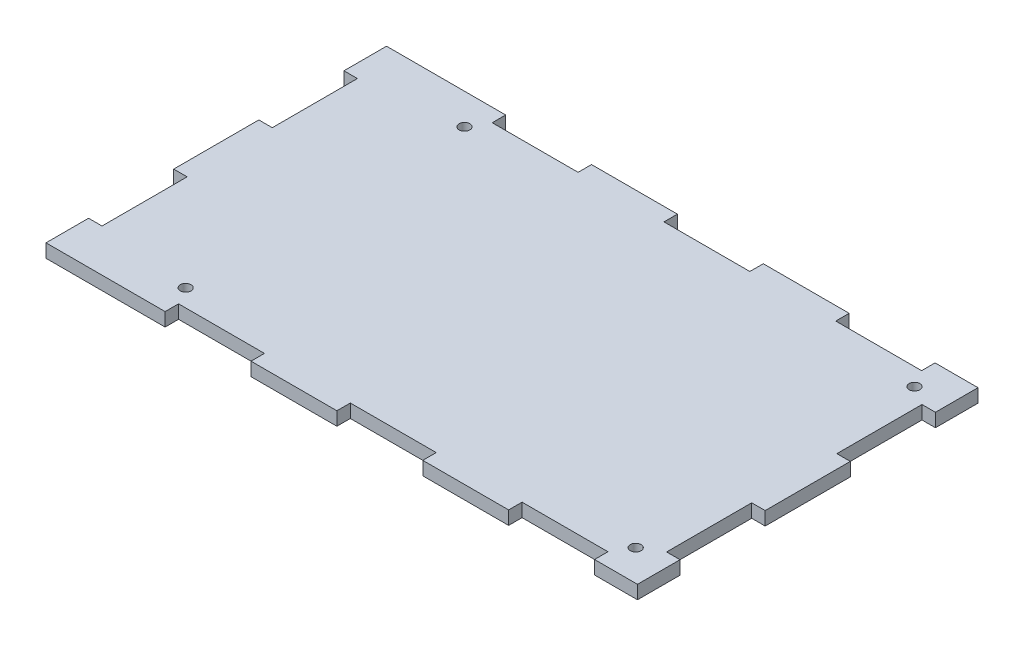
SolidWorks part; units mm, degrees
material "Acrílico (Impacto medio-alto)"
ref_plane "Alzado" through (0, 0, 0) normal (0, 0, 1) x (1, 0, 0)
ref_plane "Planta" through (0, 0, 0) normal (0, 1, 0) x (1, 0, 0)
ref_plane "Vista lateral" through (0, 0, 0) normal (1, 0, 0) x (0, 0, -1)
sketch "Croquis1" plane through (0, 0, 0) normal (0, 1, 0) x (1, 0, 0)
  line L1 (-57.5, -38) -> (57.5, -38)
  line L2 (-57.5, -38) -> (-57.5, 38)
  line L3 (-57.5, 38) -> (57.5, 38)
  line L4 (57.5, -38) -> (57.5, 38)
  line L5 (-57.5, -38) -> (57.5, 38) construction
  line L6 (-57.5, 38) -> (57.5, -38) construction
  point P0 (0, 0)
  dimension "D1" = 115
  dimension "D2" = 76
extrude "Saliente-Extruir1" add sketch "Croquis1" along normal mid plane 3
sketch "Croquis3" plane through (0, 0, 0) normal (0, 1, 0) x (1, 0, 0)
  line L0 (-57.5, -38) -> (57.5, -38) construction
  line L1 (-47.9167, -35) -> (-39.4833, -35)
  line L2 (-47.9167, -35) -> (-47.9167, -38)
  line L3 (-47.9167, -38) -> (-28.75, -38)
  line L4 (-28.75, -35) -> (-28.75, -38)
  line L5 (-39.4833, -35) -> (-39.4833, -32) construction
  line L6 (-57.5, 38) -> (-57.5, -38) construction
  line L7 (-39.4833, -32) -> (-37.1833, -32) construction
  line L8 (-37.1833, -32) -> (-37.1833, -35) construction
  line L10 (-37.1833, -35) -> (-28.75, -35)
  line L12 (-39.4833, -35) -> (-37.1833, -35)
  point P12 (-38.3333, -32)
  point P15 (-38.3333, -38)
  dimension "D2" = 3
  dimension "D3" = 9.5833
  dimension "D1" = 19.1667
  dimension "D4" = 2.3
  dimension "D5" = 3
extrude "Cortar-Extruir2" cut sketch "Croquis3" against normal through all both and the other way through all
pattern_linear "MatrizL4" count 3 spacing 38.3333 along (1, 0, 0) of "Cortar-Extruir2"
mirror "Simetría1" about plane through (0, 0, 0) normal (0, 0, 1) of "MatrizL4", "Cortar-Extruir2"
sketch "Croquis4" plane through (0, 0, 0) normal (0, 1, 0) x (1, 0, 0)
  line L0 (-57.5, 38) -> (-57.5, -38) construction
  line L1 (-57.5, 28.5) -> (-54.5, 28.5)
  line L2 (-57.5, 28.5) -> (-57.5, 9.5)
  line L3 (-57.5, 9.5) -> (-54.5, 9.5)
  line L4 (-54.5, 28.5) -> (-54.5, 20.15)
  line L5 (-47.9167, 38) -> (-57.5, 38) construction
  line L6 (-54.5, 17.85) -> (-51.5, 17.85) construction
  line L7 (-51.5, 17.85) -> (-51.5, 20.15) construction
  line L8 (-51.5, 20.15) -> (-54.5, 20.15) construction
  line L9 (-54.5, 17.85) -> (-54.5, 9.5)
  line L10 (-54.5, 20.15) -> (-54.5, 17.85)
  point P12 (-51.5, 19)
  point P13 (-57.5, 19)
  dimension "D1" = 3
  dimension "D4" = 2.3
  dimension "D5" = 3
  dimension "D2" = 9.5
  dimension "D3" = 19
extrude "Cortar-Extruir3" cut sketch "Croquis4" against normal through all both and the other way through all
pattern_linear "MatrizL5" count 2 spacing 38 along (0, 0, 1) of "Cortar-Extruir3"
mirror "Simetría2" about plane through (0, 0, 0) normal (1, 0, 0) of "MatrizL5", "Cortar-Extruir3"
sketch "Croquis2" plane through (0, 0, 0) normal (0, 1, 0) x (1, 0, 0)
  line L0 (0, 10) -> (0, 0) construction
  line L2 (0, 0) -> (-10, 0) construction
  circle A0 centre (-50.22, 31.115) radius 1.2
  circle A1 centre (-50.22, -31.115) radius 1.2
  circle A2 centre (50.22, 31.115) radius 1.2
  circle A3 centre (50.22, -31.115) radius 1.2
  dimension "D1" = 2.4
  dimension "D2" = 100.44
  dimension "D3" = 62.23
  dimension "D4" = 10
extrude "Cortar-Extruir1" cut sketch "Croquis2" against normal through all both and the other way through all
sketch "Croquis5" plane through (-57.5, 0, 0) normal (-1, 0, 0) x (0, 0, 1)
  line L0 (-38, -1.5) -> (-28.5, -1.5) construction
  line L1 (-28.5, -1.5) -> (-28.5, 1.5) construction
  line L2 (-28.5, 1.5) -> (-38, 1.5) construction
  line L3 (-38, 1.5) -> (-38, -1.5) construction
  line L4 (38, 1.5) -> (28.5, 1.5) construction
  line L5 (28.5, 1.5) -> (28.5, -1.5) construction
  line L6 (28.5, -1.5) -> (38, -1.5) construction
  line L7 (38, -1.5) -> (38, 1.5) construction
  line L8 (-38, -1.5) -> (-28.5, -1.5)
  line L9 (-28.5, -1.5) -> (-28.5, 1.5)
  line L10 (-28.5, 1.5) -> (-38, 1.5)
  line L11 (-38, 1.5) -> (-38, -1.5)
  line L12 (38, 1.5) -> (28.5, 1.5)
  line L13 (28.5, 1.5) -> (28.5, -1.5)
  line L14 (28.5, -1.5) -> (38, -1.5)
  line L15 (38, -1.5) -> (38, 1.5)
  line L20 (-9.5, -1.5) -> (9.5, -1.5)
  line L21 (9.5, -1.5) -> (9.5, 1.5)
  line L22 (9.5, 1.5) -> (-9.5, 1.5)
  line L23 (-9.5, 1.5) -> (-9.5, -1.5)
  line L24 (-9.5, -1.5) -> (9.5, -1.5)
  line L25 (9.5, -1.5) -> (9.5, 1.5)
  line L26 (9.5, 1.5) -> (-9.5, 1.5)
  line L27 (-9.5, 1.5) -> (-9.5, -1.5)
  dimension "D1" = 0
extrude "Saliente-Extruir2" add sketch "Croquis5" along normal blind 17
sketch "Croquis6" plane through (-54.5, 0, 0) normal (-1, 0, 0) x (0, 0, 1)
  line L32 (9.5, 1.5) -> (9.5, -1.5) construction
  line L33 (9.5, -1.5) -> (28.5, -1.5) construction
  line L34 (28.5, -1.5) -> (28.5, 1.5) construction
  line L35 (28.5, 1.5) -> (9.5, 1.5) construction
  line L36 (-28.5, 1.5) -> (-28.5, -1.5) construction
  line L37 (-28.5, -1.5) -> (-9.5, -1.5) construction
  line L38 (-9.5, -1.5) -> (-9.5, 1.5) construction
  line L39 (-9.5, 1.5) -> (-28.5, 1.5) construction
  line L40 (9.5, 1.5) -> (9.5, -1.5)
  line L41 (9.5, -1.5) -> (28.5, -1.5)
  line L42 (28.5, -1.5) -> (28.5, 1.5)
  line L43 (28.5, 1.5) -> (9.5, 1.5)
  line L44 (-28.5, 1.5) -> (-28.5, -1.5)
  line L45 (-28.5, -1.5) -> (-9.5, -1.5)
  line L46 (-9.5, -1.5) -> (-9.5, 1.5)
  line L47 (-9.5, 1.5) -> (-28.5, 1.5)
extrude "Saliente-Extruir3" add sketch "Croquis6" along normal offset from surface (17 mm away) 3 up to face at (-74.5, 0, 33.25)
equation "\"grosor\"= 3mm'Acrilico"
equation "\"D1@Croquis1\"=\"W\"+2*\"grosor\""
equation "\"D1@Saliente-Extruir1\"=\"grosor\""
equation "\"longInsert\"= 100.44mm"
equation "\"shortInsert\"= 62.23mm"
equation "\"D2@Croquis2\"=\"longInsert\""
equation "\"D3@Croquis2\"=\"shortInsert\""
equation "\"longInstance\"= 3"
equation "\"W\"= 109mm"
equation "\"H\"= 70mm"
equation "\"D2@Croquis1\"=\"H\"+2*\"grosor\""
equation "\"D2@Croquis3\"=\"grosor\""
equation "\"shortInstance\"= 2"
equation "\"D1@Croquis4\"=\"grosor\""
equation "\"D2@Croquis4\"=\"cH\"/(4*\"shortInstance\")"
equation "\"D3@Croquis4\"=\"cH\"/(2*\"shortInstance\")"
equation "\"cW\"= \"W\" + 2 * \"grosor\"'Largo compensado con acrilico"
equation "\"cH\"= \"H\" + 2 * \"grosor\"'Ancho compensado"
equation "\"D3@Croquis3\"=\"cW\"/(4*\"longInstance\")"
equation "\"D1@Croquis3\"=\"cW\"/(2*\"longInstance\")"
equation "\"D1@MatrizL4\"=\"longInstance\""
equation "\"D3@MatrizL4\"=\"cW\"/(\"longInstance\")"
equation "\"D3@MatrizL5\"=\"cH\"/\"shortInstance\""
equation "\"D1@MatrizL5\"=\"shortInstance\""
equation "\"L\"= 70mm"
equation "\"D5@Croquis3\"=\"grosor\""
equation "\"D5@Croquis4\"=\"grosor\""
equation "\"wallInstance\"= 2"
equation "\"MACHUELO\"=2.3"
equation "\"D4@Croquis3\"=\"MACHUELO\""
equation "\"D4@Croquis4\"=\"MACHUELO\""
equation "\"D19@Saliente-Extruir3\"=\"grosor\""
equation "\"D1@Saliente-Extruir3\"=\"grosor\""
equation "\"D1@Saliente-Extruir4\"=\"grosor\""
